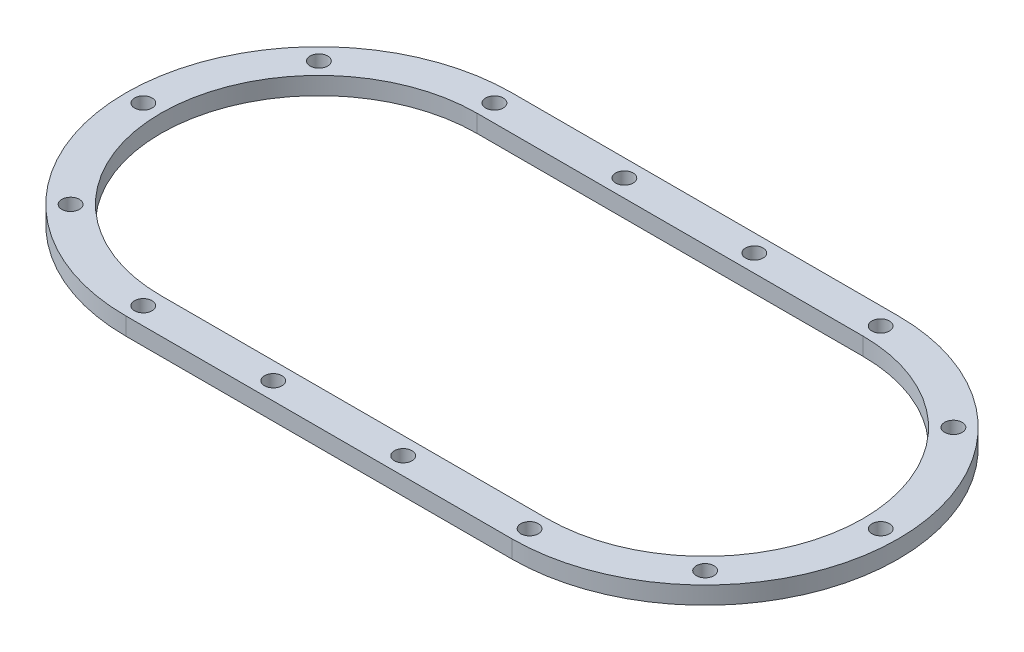
SolidWorks part; units mm, degrees
ref_plane "Front Plane" through (0, 0, 0) normal (0, 0, 1) x (1, 0, 0)
ref_plane "Top Plane" through (0, 0, 0) normal (0, 1, 0) x (1, 0, 0)
ref_plane "Right Plane" through (0, 0, 0) normal (1, 0, 0) x (0, 0, -1)
sketch "Sketch1" plane through (0, 0, 0) normal (0, 1, 0) x (1, 0, 0)
  line L0 (-110, 0) -> (110, 0) construction
  line L1 (-110, 110) -> (110, 110)
  line L2 (-110, -110) -> (110, -110)
  line L3 (-110, 0) -> (110, 0) construction
  line L4 (-110, 90) -> (110, 90)
  line L5 (-110, -90) -> (110, -90)
  line L6 (0, 110) -> (0, -110) construction
  arc A0 (-110, 110) -> (-110, -110) centre (-110, 0) ccw
  arc A1 (110, -110) -> (110, 110) centre (110, 0) ccw
  arc A2 (-110, 90) -> (-110, -90) centre (-110, 0) ccw
  arc A3 (110, -90) -> (110, 90) centre (110, 0) ccw
  point P2 (0, 0)
  point P10 (0, 0)
  dimension "D2" = 110
  dimension "D3" = 90
  dimension "D1" = 220
  dimension "D4" = 220
extrude "Boss-Extrude1" add sketch "Sketch1" along normal blind 10
hole_wizard "Ø10.0mm Dowel Hole6" positions "3DSketch12" profile "Sketch12" hole size "Ø10.0" standard "ANSI Metric" end condition through all
sketch3d "3DSketch12"
  line L0 (-110, 10, -110) -> (-110, 10, -90) construction
  point P0 (-110, 10, -100)
  point P9 (-110, 10, -100)
sketch "Sketch12" plane through (-110, 10, -100) normal (1, 0, 0) x (0, 0, 1)
  line L0 (0, 0) -> (0, 10)
  line L1 (0, 10) -> (5, 10)
  line L2 (5, 10) -> (5, 0)
  line L5 (5, 0) -> (0, 0)
  line L11 (0, -6.35) -> (0, 107.95) construction
  dimension "Thru Hole Dia." = 10
  dimension "Thru Hole Depth" = 10
pattern_circular "CirPattern2" count 5 over 180 about axis through (-110, 0, 0) along (0, 1, 0) of "Ø10.0mm Dowel Hole6"
mirror "Mirror2" about plane through (0, 0, 0) normal (1, 0, 0) of "CirPattern2", "Ø10.0mm Dowel Hole6"
pattern_linear "LPattern1" count 3 spacing 74 along (1, 0, 0) of "Ø10.0mm Dowel Hole6"
mirror "Mirror3" about plane through (0, 0, 0) normal (0, 0, 1) of "LPattern1"
